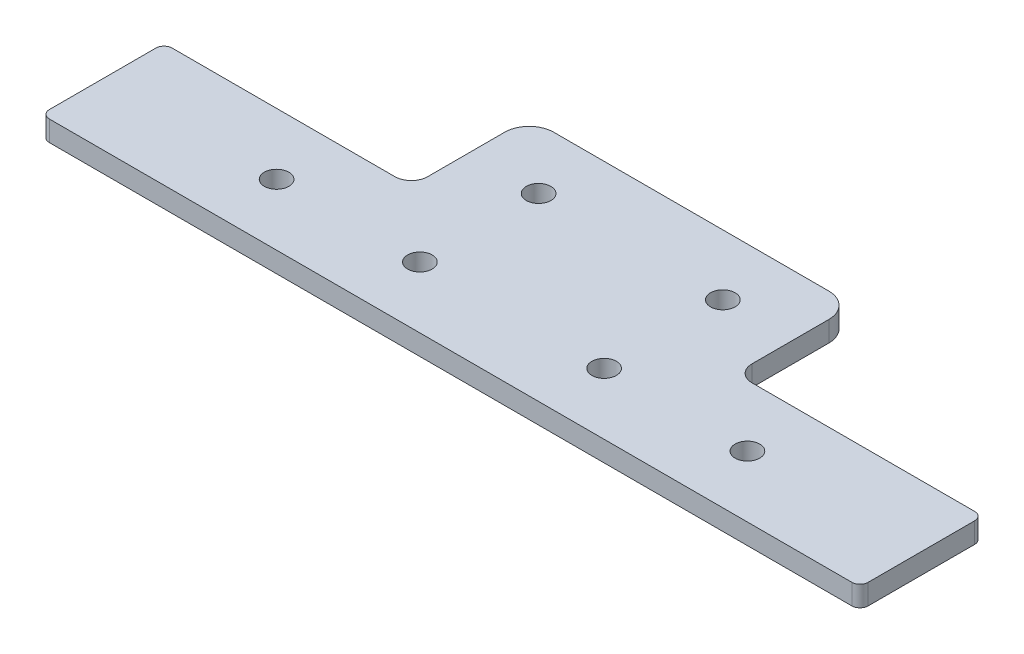
SolidWorks part; units mm, degrees
material "Alum Plate"
ref_plane "Front Plane" through (0, 0, 0) normal (0, 0, 1) x (1, 0, 0)
ref_plane "Top Plane" through (0, 0, 0) normal (0, 1, 0) x (1, 0, 0)
ref_plane "Right Plane" through (0, 0, 0) normal (1, 0, 0) x (0, 0, -1)
other "Bounding Box"
ref_plane "Default Plane" through (13.8565, 3.175, 6.7999) normal (0, -1, 0) x (-1, 0, 0)
sketch "Sketch1" plane through (0, 0, 0) normal (0, 1, 0) x (1, 0, 0)
  line L1 (-63.5, -9.525) -> (63.5, -9.525)
  line L2 (-63.5, -9.525) -> (-63.5, 9.525)
  line L3 (-63.5, 9.525) -> (63.5, 9.525)
  line L4 (63.5, -9.525) -> (63.5, 9.525)
  line L5 (-63.5, -9.525) -> (63.5, 9.525) construction
  line L6 (-63.5, 9.525) -> (63.5, -9.525) construction
  point P0 (0, 0)
  dimension "D1" = 19.05
  dimension "D2" = 127
extrude "Boss-Extrude1" add sketch "Sketch1" along normal blind 3.175
sketch "Sketch3" plane through (0, 3.175, 0) normal (0, 1, 0) x (1, 0, 0)
  line L0 (63.5, 9.525) -> (-63.5, 9.525) construction
  line L1 (-25.146, 9.525) -> (25.146, 9.525)
  line L2 (-25.146, 9.525) -> (-25.146, 27.813)
  line L3 (-25.146, 27.813) -> (25.146, 27.813)
  line L4 (25.146, 9.525) -> (25.146, 27.813)
  line L5 (-25.146, 9.525) -> (25.146, 27.813) construction
  line L6 (-25.146, 27.813) -> (25.146, 9.525) construction
  point P4 (0, 18.669)
  dimension "D1" = 50.292
  dimension "D2" = 18.288
extrude "Boss-Extrude2" add sketch "Sketch3" against normal through all
sketch "Sketch2" plane through (0, 3.175, 0) normal (0, 1, 0) x (1, 0, 0)
  line L0 (-36.5125, 0) -> (-14.2875, 0) construction
  line L1 (-14.2875, 0) -> (-14.2875, 18.415) construction
  line L2 (-36.5125, 0) -> (-36.5125, 9.525) construction
  line L3 (63.5, 9.525) -> (25.146, 9.525) construction
  line L4 (-14.2875, 0) -> (14.2875, 0) construction
  line L5 (-14.2875, 18.415) -> (14.2875, 18.415) construction
  line L6 (36.5125, 0) -> (36.5125, 9.525) construction
  line L7 (14.2875, 0) -> (36.5125, 0) construction
  line L8 (-25.146, 9.525) -> (-63.5, 9.525) construction
  line L9 (-14.2875, 18.415) -> (-14.2875, 27.813) construction
  line L10 (25.146, 27.813) -> (-25.146, 27.813) construction
  line L11 (14.2875, 18.415) -> (14.2875, 9.525) construction
  line L12 (63.5, 9.525) -> (25.146, 9.525) construction
  circle A0 centre (-36.5125, 0) radius 1.905
  circle A1 centre (36.5125, 0) radius 1.905
  circle A2 centre (-14.2875, 0) radius 1.905
  circle A3 centre (14.2875, 0) radius 1.905
  circle A4 centre (-14.2875, 18.415) radius 1.905
  circle A5 centre (14.2875, 18.415) radius 1.905
  point P11 (0, 0)
  dimension "D1" = 3.81
  dimension "D2" = 28.575
  dimension "D3" = 22.225
  dimension "D4" = 8.89
extrude "Cut-Extrude1" cut sketch "Sketch2" against normal through all
fillet "Fillet1" radius 1.27 4 edges at (63.5, 1.5875, -9.525) (63.5, 1.5875, 9.525) (-63.5, 1.5875, -9.525) (-63.5, 1.5875, 9.525)
fillet "Fillet2" radius 2.54 2 edges at (25.146, 1.5875, -9.525) (-25.146, 1.5875, -9.525)
fillet "Fillet3" radius 3.81 2 edges at (-25.146, 1.5875, -27.813) (25.146, 1.5875, -27.813)
